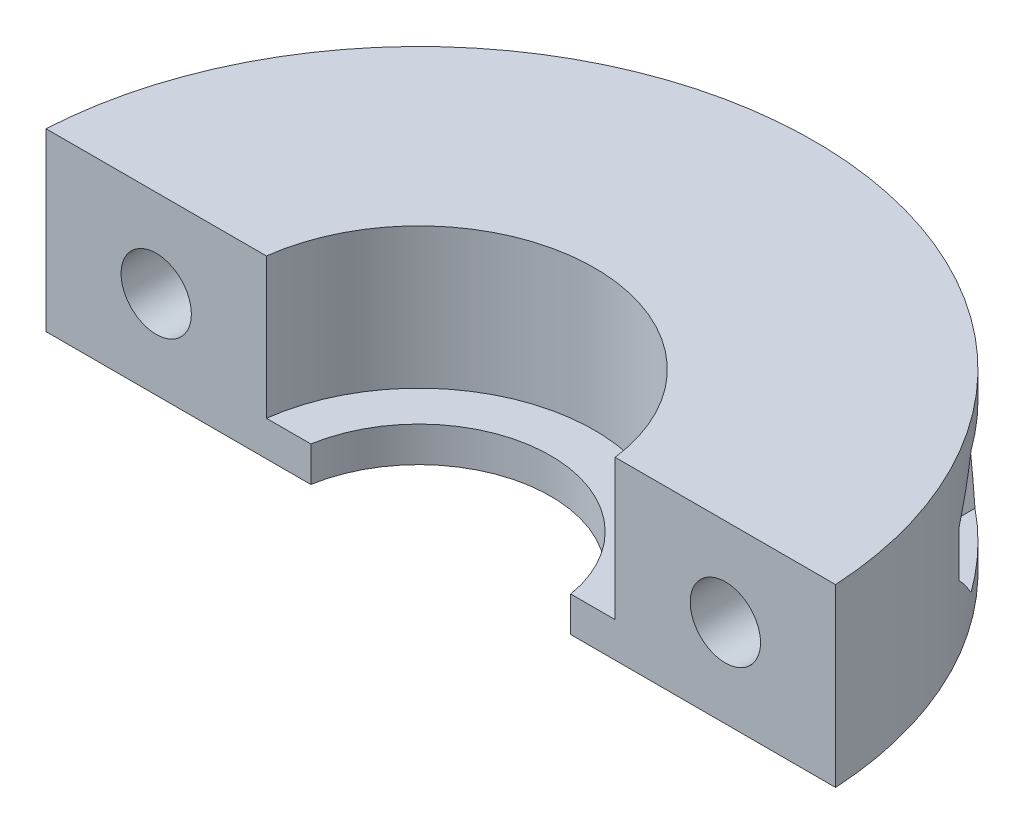
SolidWorks part; units mm, degrees
material "ABS"
ref_plane "Front Plane" through (0, 0, 0) normal (0, 0, 1) x (1, 0, 0)
ref_plane "Top Plane" through (0, 0, 0) normal (0, 1, 0) x (1, 0, 0)
ref_plane "Right Plane" through (0, 0, 0) normal (1, 0, 0) x (0, 0, -1)
sketch "Sketch1" plane through (0, 0, 0) normal (0, 1, 0) x (1, 0, 0)
  circle A0 centre (0, 0) radius 8
  circle A1 centre (0, 0) radius 18
  dimension "D1" = 16
  dimension "D2" = 10
extrude "Boss-Extrude1" add sketch "Sketch1" along normal blind 8
ref_plane "Plane1" through (0, 4, 0) normal (0, 1, 0) x (1, 0, 0)
sketch "Sketch2" plane through (0, 0, 0) normal (0, 1, 0) x (1, 0, 0)
  circle A0 centre (0, 0) radius 8
  circle A1 centre (0, 0) radius 6
  dimension "D1" = 16
  dimension "D2" = 12
extrude "Boss-Extrude2" add sketch "Sketch2" along normal blind 1.6
sketch "Sketch3" plane through (0, 8, 0) normal (0, 1, 0) x (1, 0, 0)
  line L0 (-20, 1) -> (20, 1)
  line L1 (20, 1) -> (20, -19)
  line L2 (20, -19) -> (-20, -19)
  line L3 (-20, -19) -> (-20, 1)
  line L4 (0, 0) -> (0, 1) construction
  dimension "D1" = 20
  dimension "D2" = 1
  dimension "D3" = 40
extrude "Cut-Extrude1" cut sketch "Sketch3" against normal through all
sketch "Sketch5" plane through (0, 0, -1) normal (0, 0, 1) x (1, 0, 0)
  line L0 (-7.9373, 8) -> (-17.9722, 8) construction
  line L1 (-12.9547, 8) -> (-12.9547, 4) construction
  line L2 (-17.9722, 4) -> (-12.9547, 4) construction
  line L3 (-17.9722, 0) -> (-17.9722, 8) construction
  line L4 (12.9547, 8) -> (12.9547, 4) construction
  line L5 (17.9722, 8) -> (7.9373, 8) construction
  line L6 (12.9547, 4) -> (17.9722, 4) construction
  line L7 (17.9722, 8) -> (17.9722, 0) construction
  circle A0 centre (-12.9547, 4) radius 1.6
  circle A1 centre (12.9547, 4) radius 1.6
  dimension "D1" = 3.2
extrude "Cut-Extrude2" cut sketch "Sketch5" against normal up to next
sketch "Sketch6" plane through (0, 0, -1) normal (0, 0, 1) x (1, 0, 0)
  line L1 (-9.7216, 4) -> (-11.3381, 6.8)
  line L2 (-11.3381, 6.8) -> (-14.5713, 6.8)
  line L3 (-14.5713, 6.8) -> (-16.1879, 4)
  line L4 (-16.1879, 4) -> (-14.5713, 1.2)
  line L5 (-14.5713, 1.2) -> (-11.3381, 1.2)
  line L6 (-11.3381, 1.2) -> (-9.7216, 4)
  line L7 (16.1879, 4) -> (14.5713, 6.8)
  line L8 (14.5713, 6.8) -> (11.3381, 6.8)
  line L9 (11.3381, 6.8) -> (9.7216, 4)
  line L10 (9.7216, 4) -> (11.3381, 1.2)
  line L11 (11.3381, 1.2) -> (14.5713, 1.2)
  line L12 (14.5713, 1.2) -> (16.1879, 4)
  circle A0 centre (-12.9547, 4) radius 2.8 construction
  circle A1 centre (12.9547, 4) radius 2.8 construction
  dimension "D1" = 5.6
extrude "Cut-Extrude3" cut sketch "Sketch6" against normal up to next from offset 8
